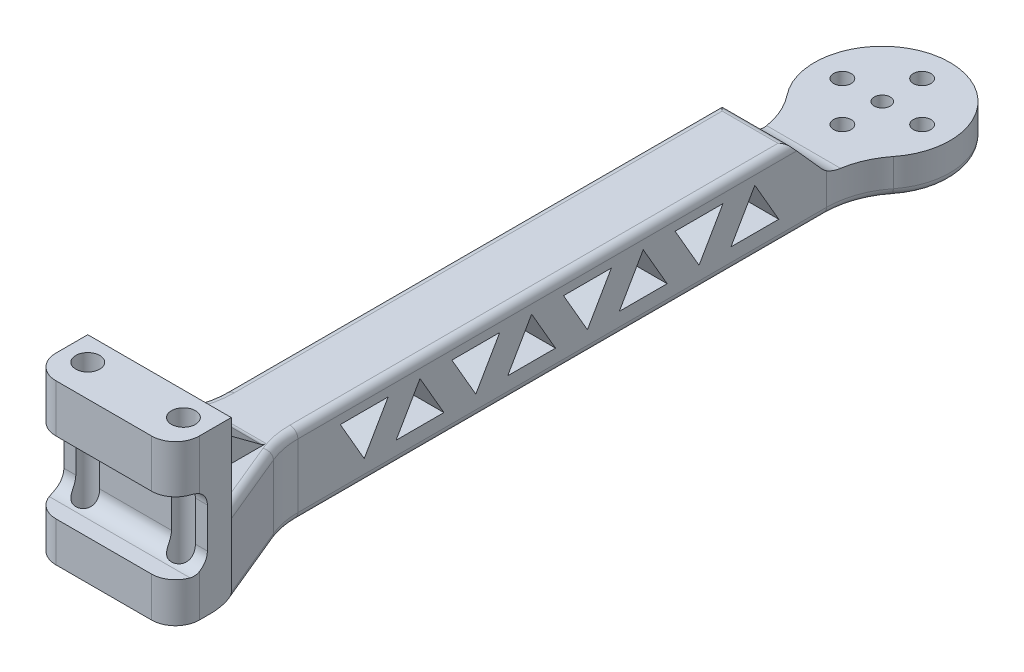
SolidWorks part; units mm, degrees
ref_plane "Front Plane" through (0, 0, 0) normal (0, 0, 1) x (1, 0, 0)
ref_plane "Top Plane" through (0, 0, 0) normal (0, 1, 0) x (1, 0, 0)
ref_plane "Right Plane" through (0, 0, 0) normal (1, 0, 0) x (0, 0, -1)
sketch "Sketch1" plane through (0, 0, 0) normal (0, 1, 0) x (1, 0, 0)
  line L0 (9.3708, 0) -> (9.3708, 74.7675) construction
  line L1 (3.3708, 0) -> (15.3708, 0)
  line L2 (18.3708, 3) -> (18.3708, 7)
  line L3 (13.8708, 86.162) -> (13.8708, 19.8531)
  line L4 (18.3708, 7) -> (14.632, 16.0263)
  line L5 (0.3708, 7) -> (4.1096, 16.0263)
  line L6 (0.3708, 3) -> (0.3708, 7)
  line L7 (4.8708, 86.162) -> (4.8708, 19.8531)
  arc A0 (15.3708, 0) -> (18.3708, 3) centre (15.3708, 3) ccw
  arc A1 (14.632, 16.0263) -> (13.8708, 19.8531) centre (23.8708, 19.8531) cw
  arc A2 (4.1096, 16.0263) -> (4.8708, 19.8531) centre (-5.1292, 19.8531) ccw
  arc A3 (3.3708, 0) -> (0.3708, 3) centre (3.3708, 3) cw
  arc A4 (16.0329, 92.3723) -> (2.7086, 92.3723) centre (9.3708, 97.6511) ccw
  arc A5 (13.8708, 86.162) -> (16.0329, 92.3723) centre (23.8708, 86.162) cw
  arc A6 (4.8708, 86.162) -> (2.7086, 92.3723) centre (-5.1292, 86.162) ccw
  point P7 (18.3708, 0)
  point P18 (0.3708, 0)
  point P23 (13.8708, 90.44)
  point P26 (4.8708, 90.44)
  dimension "D4" = 3
  dimension "D5" = 10
  dimension "D8" = 17
  dimension "D9" = 10
  dimension "D1" = 90.44
  dimension "D2" = 9
  dimension "D3" = 7
  dimension "D6" = 22.5
  dimension "D7" = 9
extrude "Boss-Extrude1" add sketch "Sketch1" along normal blind 10
sketch "Sketch2" plane through (0, 0, 0) normal (1, 0, 0) x (0, 0, -1)
  line L0 (79.6956, 12.0444) -> (85.5466, 5.5004)
  line L1 (87.7831, 4.5) -> (106.1511, 4.5)
  line L2 (106.1511, 4.5) -> (106.1511, 14.1345)
  line L3 (106.1511, 14.1345) -> (79.6956, 14.1345)
  line L4 (79.6956, 14.1345) -> (79.6956, 12.0444)
  line L5 (92.3723, 0) -> (106.1511, 0) construction
  line L6 (106.1511, 0) -> (106.1511, 10) construction
  arc A0 (85.5466, 5.5004) -> (87.7831, 4.5) centre (87.7831, 7.5) ccw
  point P11 (86.4411, 4.5)
  dimension "D4" = 3
  dimension "D1" = 4.5
  dimension "D2" = 19.71
  dimension "D3" = 131.8
extrude "Cut-Extrude1" cut sketch "Sketch2" against normal through all both and the other way through all
sketch "Sketch3" plane through (0, 4.5, 0) normal (0, 1, 0) x (1, 0, 0)
  circle A0 centre (9.3708, 97.6511) radius 5 construction
  arc A1 (16.0329, 92.3723) -> (2.7086, 92.3723) centre (9.3708, 97.6511) ccw construction
  circle A2 centre (9.3708, 97.6511) radius 1
  circle A3 centre (9.3708, 102.6511) radius 1.1
  circle A4 centre (14.3708, 97.6511) radius 1.1
  circle A5 centre (9.3708, 92.6511) radius 1.1
  circle A6 centre (4.3708, 97.6511) radius 1.1
  point P17 (9.3708, 97.6511)
  dimension "D1" = 10
  dimension "D2" = 2
  dimension "D3" = 2.2
  dimension "D4" = 4
extrude "Cut-Extrude2" cut sketch "Sketch3" against normal through all both
sketch "Sketch4" plane through (0, 10, 0) normal (0, 1, 0) x (1, 0, 0)
  line L0 (18.3708, 7) -> (0.3708, 7)
  line L1 (0.3708, 7) -> (0.3708, 3)
  line L2 (3.3708, 0) -> (15.3708, 0)
  line L3 (18.3708, 3) -> (18.3708, 7)
  arc A0 (0.3708, 3) -> (3.3708, 0) centre (3.3708, 3) ccw
  arc A1 (15.3708, 0) -> (18.3708, 3) centre (15.3708, 3) ccw
extrude "Boss-Extrude2" add sketch "Sketch4" along normal blind 10
sketch "Sketch5" plane through (0, 20, 0) normal (0, 1, 0) x (1, 0, 0)
  line L0 (0.3708, 7) -> (0.3708, 3) construction
  line L1 (3.3708, 0) -> (15.3708, 0) construction
  circle A0 centre (3.3708, 4) radius 1.5
  circle A1 centre (15.3708, 4) radius 1.5
  dimension "D1" = 3
  dimension "D2" = 3
  dimension "D3" = 3
  dimension "D4" = 4
  dimension "D5" = 12
extrude "Cut-Extrude3" cut sketch "Sketch5" against normal through all
sketch "Sketch6" plane through (18.3708, 0, 0) normal (1, 0, 0) x (0, 0, -1)
  line L0 (0, 14) -> (2, 14)
  line L1 (0, 20) -> (0, 0) construction
  line L2 (4, 12) -> (4, 7)
  line L3 (2, 5) -> (0, 5)
  line L4 (0, 5) -> (0, 14)
  line L5 (3, 20) -> (0, 20) construction
  arc A0 (4, 7) -> (2, 5) centre (2, 7) cw
  arc A1 (2, 14) -> (4, 12) centre (2, 12) cw
  point P10 (4, 5)
  point P13 (4, 14)
  dimension "D4" = 2
  dimension "D1" = 4
  dimension "D2" = 9
  dimension "D3" = 6
extrude "Cut-Extrude4" cut sketch "Sketch6" against normal through all
sketch "Sketch7" plane through (4.8708, 0, 0) normal (-1, 0, 0) x (0, 0, 1)
  line L0 (-81.5235, 10) -> (-19.8531, 10) construction
  line L1 (-77.1735, 7.8962) -> (-80.1735, 2.7)
  line L2 (-80.1735, 2.7) -> (-74.1735, 2.7)
  line L3 (-74.1735, 2.7) -> (-77.1735, 7.8962)
  line L4 (-73.1735, 7.9) -> (-70.1735, 2.7038)
  line L5 (-70.1735, 2.7038) -> (-67.1735, 7.9)
  line L6 (-67.1735, 7.9) -> (-73.1735, 7.9)
  line L7 (-86.162, 0) -> (-19.8531, 0) construction
  line L8 (-63.1735, 7.8962) -> (-66.1735, 2.7)
  line L9 (-66.1735, 2.7) -> (-60.1735, 2.7)
  line L10 (-60.1735, 2.7) -> (-63.1735, 7.8962)
  line L11 (-59.1735, 7.9) -> (-56.1735, 2.7038)
  line L12 (-56.1735, 2.7038) -> (-53.1735, 7.9)
  line L13 (-53.1735, 7.9) -> (-59.1735, 7.9)
  line L14 (-49.1735, 7.8962) -> (-52.1735, 2.7)
  line L15 (-52.1735, 2.7) -> (-46.1735, 2.7)
  line L16 (-46.1735, 2.7) -> (-49.1735, 7.8962)
  line L17 (-45.1735, 7.9) -> (-42.1735, 2.7038)
  line L18 (-42.1735, 2.7038) -> (-39.1735, 7.9)
  line L19 (-39.1735, 7.9) -> (-45.1735, 7.9)
  line L20 (-35.1735, 7.8962) -> (-38.1735, 2.7)
  line L21 (-38.1735, 2.7) -> (-32.1735, 2.7)
  line L22 (-32.1735, 2.7) -> (-35.1735, 7.8962)
  line L23 (-31.1735, 7.9) -> (-28.1735, 2.7038)
  line L24 (-28.1735, 2.7038) -> (-25.1735, 7.9)
  line L25 (-25.1735, 7.9) -> (-31.1735, 7.9)
  circle A0 centre (-77.1735, 4.4321) radius 1.7321 construction
  circle A1 centre (-70.1735, 6.1679) radius 1.7321 construction
  dimension "D1" = 6
  dimension "D2" = 6
  dimension "D3" = 5.2
  dimension "D4" = 7
  dimension "D5" = 4.35
  dimension "D6" = 2.7
  dimension "D7" = 4
extrude "Cut-Extrude5" cut sketch "Sketch7" against normal through all
sketch "Sketch9" plane through (0.3708, 0, 0) normal (-1, 0, 0) x (0, 0, 1)
  line L0 (-7, 16.6715) -> (-7, 10)
  line L1 (-7, 20) -> (-7, 10) construction
  line L2 (-7, 10) -> (-16.0263, 10)
  line L3 (-16.0263, 10) -> (-7, 10) construction
  line L4 (-16.0263, 10) -> (-7, 16.6715)
extrude "Boss-Extrude3" add sketch "Sketch9" against normal blind 8 from offset 5 offset against normal yes
fillet "Fillet2" radius 1 16 edges at (16.5014, 10, -11.5131) (14.0629, 10, -17.9022) (16.5014, 0, -11.5131) (14.0629, 0, -17.9022) (13.8708, 0, -53.0075) (14.4268, 0, -89.45) (9.3708, 0, -106.1511) (4.3148, 0, -89.45) (2.2402, 0, -11.5131) (4.6786, 0, -17.9022) (2.2402, 10, -11.5131) (4.6786, 10, -17.9022) (13.8708, 10, -50.6883) (4.8708, 0, -53.0075) (4.8708, 10, -50.6883) (9.3708, 10, -81.5235)
fillet "Fillet3" radius 1 2 edges at (9.3708, 16.6715, -7) (9.3708, 10, -16.0263)
sketch "Sketch11" plane through (0, 0, 0) normal (0, -1, 0) x (1, 0, 0)
  line L6 (3.3708, 0) -> (15.3708, 0) construction
  circle A0 centre (9.3708, -62.6443) radius 1.25
  point P10 (9.3708, 0)
  dimension "D1" = 2.5
extrude "Cut-Extrude12" cut sketch "Sketch11" against normal blind 4
